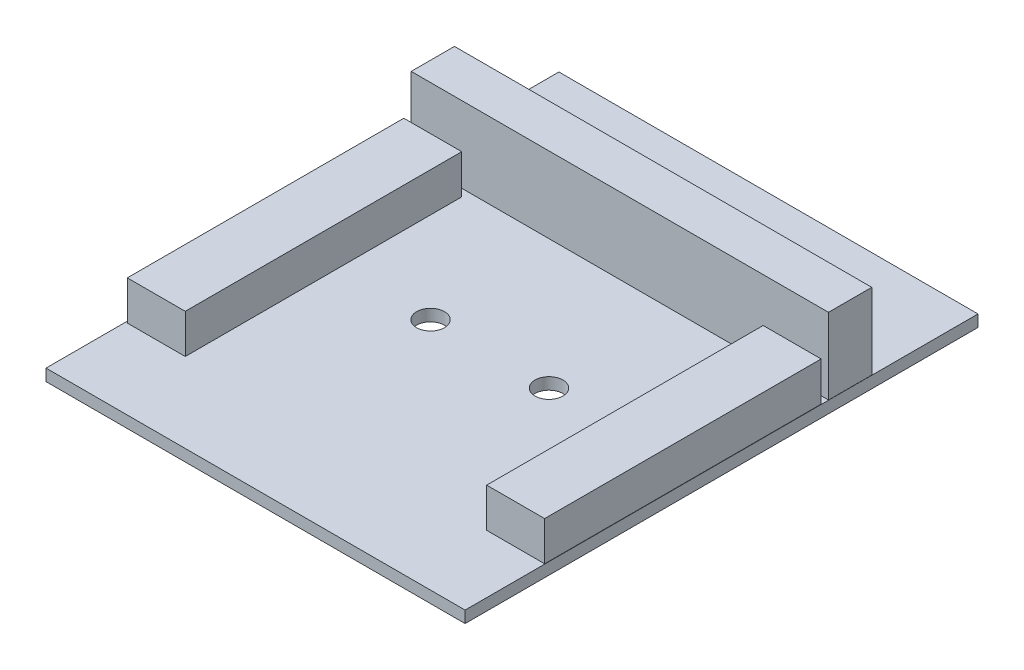
SolidWorks part; units mm, degrees
ref_plane "Plan de face" through (0, 0, 0) normal (0, 0, 1) x (1, 0, 0)
ref_plane "Plan de dessus" through (0, 0, 0) normal (0, 1, 0) x (1, 0, 0)
ref_plane "Plan de droite" through (0, 0, 0) normal (1, 0, 0) x (0, 0, -1)
sketch "Esquisse1" plane through (0, 0, 0) normal (0, 1, 0) x (1, 0, 0)
  line L1 (0, 0) -> (57.1474, 0)
  line L2 (0, 0) -> (0, 69.9356)
  line L3 (0, 69.9356) -> (57.1474, 69.9356)
  line L4 (57.1474, 0) -> (57.1474, 69.9356)
  circle A0 centre (20.5, 31.9356) radius 1.9
  circle A1 centre (36.6474, 31.9356) radius 1.9
  point P17 (30.4422, 34.2183)
  dimension "D1" = 38
  dimension "D2" = 38
  dimension "D3" = 20.5
  dimension "D4" = 20.5
  dimension "D5" = 16.1474
extrude "Boss.-Extru.7" add sketch "Esquisse1" along normal blind 1.6
sketch "Esquisse6" plane through (0, 1.6, 0) normal (0, 1, 0) x (1, 0, 0)
  line L0 (49.2059, 48.5846) -> (57.1059, 48.5846)
  line L1 (0.2285, 48.56) -> (8.1285, 48.56)
  line L2 (0.2285, 48.56) -> (0.2285, 10.86)
  line L3 (0.2285, 10.86) -> (8.1285, 10.86)
  line L4 (8.1285, 48.56) -> (8.1285, 10.86)
  line L5 (49.2059, 48.5846) -> (49.2059, 10.8846)
  line L6 (49.2059, 10.8846) -> (57.1059, 10.8846)
  line L7 (57.1059, 48.5846) -> (57.1059, 10.8846)
sketch "Esquisse7" plane through (0, 1.6, 0) normal (0, 1, 0) x (1, 0, 0)
  line L1 (0.2206, 55.4756) -> (57.1206, 55.4756)
  line L2 (0.2206, 55.4756) -> (0.2206, 49.5756)
  line L3 (0.2206, 49.5756) -> (57.1206, 49.5756)
  line L4 (57.1206, 55.4756) -> (57.1206, 49.5756)
  line L5 (57.1474, 69.9356) -> (0, 69.9356) construction
  dimension "D1" = 14.46
extrude "Boss.-Extru.8" add sketch "Esquisse6" along normal blind 5.34
extrude "Boss.-Extru.9" add sketch "Esquisse7" along normal blind 10.36
